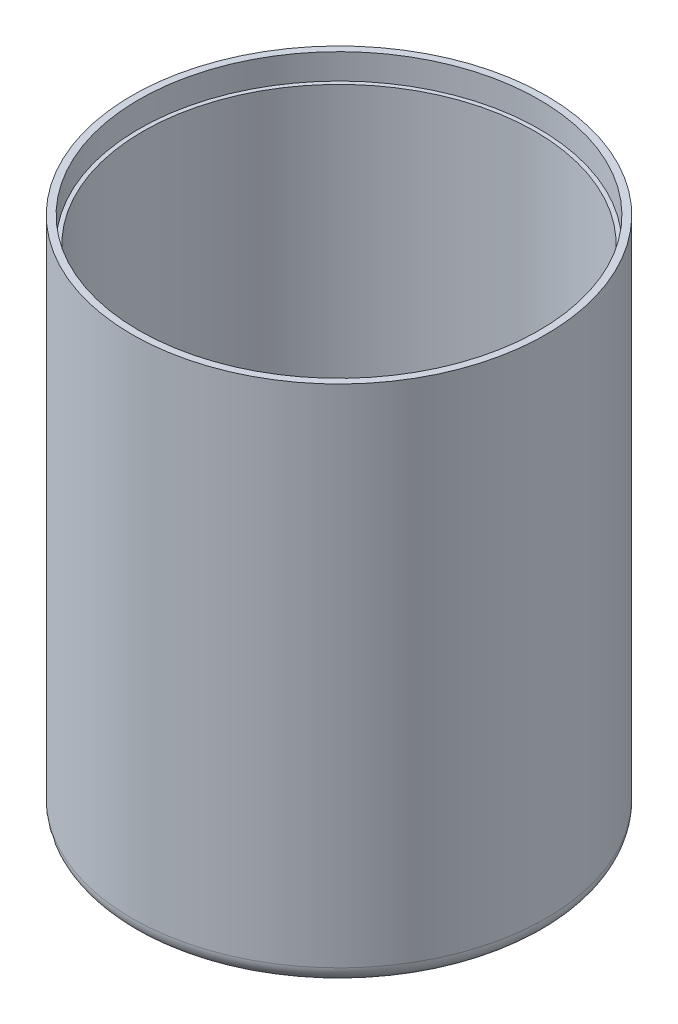
SolidWorks part; units mm, degrees
ref_plane "前视基准面" through (0, 0, 0) normal (0, 0, 1) x (1, 0, 0)
ref_plane "上视基准面" through (0, 0, 0) normal (0, 1, 0) x (1, 0, 0)
ref_plane "右视基准面" through (0, 0, 0) normal (1, 0, 0) x (0, 0, -1)
sketch "草图3" plane through (0, 0, 0) normal (0, 0, 1) x (1, 0, 0)
  line L0 (3.225, -1.7) -> (3.225, 0)
  line L1 (3.225, 0) -> (12.2, 0)
  line L2 (12.2, 0) -> (12.2, 30.8)
  line L3 (0, -2.2801) -> (0, 32.8942) construction
  dimension "D1" = 1.7
  dimension "D2" = 12.2
  dimension "D3" = 3.225
  dimension "D4" = 30.8
revolve "旋转-薄壁1" add sketch "草图3" angle 360 about L3 wall 0.65
sketch "草图8" plane through (0, 0, 0) normal (0, -1, 0) x (1, 0, 0)
  line L0 (0, -4.2367) -> (0, 3.6419) construction
  circle A0 centre (-8.5, 0) radius 1
  circle A1 centre (8.5, 0) radius 1
  dimension "D2" = 2
  dimension "D1" = 17
extrude "切除-拉伸1" cut sketch "草图8" against normal through all
sketch "草图9" plane through (0, 0, 0) normal (0, 0, 1) x (1, 0, 0)
  line L0 (-9.5, 0.65) -> (-9.5, 1.05)
  line L1 (-8.5, 2.0071) -> (-8.5, -0.8567) construction
  line L2 (-7.5, 0) -> (-7.5, 0.65) construction
  line L3 (-9.5, 0.65) -> (-9.5, 0) construction
  dimension "D1" = 0.4
revolve "旋转-薄壁2" add sketch "草图9" angle 360 about L1 wall 0.43
hole_wizard "M3 螺纹孔2" positions "草图11" profile "草图12" tap size "M3" standard "GB" end condition through all
sketch "草图11" plane through (0, 0, 0) normal (0, -1, 0) x (-1, 0, 0)
  point P0 (8.5, 0)
  point P3 (-8.5, 0)
sketch "草图12" plane through (-8.5, 0, 0) normal (1, 0, 0) x (0, 0, -1)
  line L0 (0, 0) -> (0, 30.8)
  line L1 (0, 30.8) -> (1.25, 30.8)
  line L2 (1.25, 30.8) -> (1.25, 0)
  line L5 (1.25, 0) -> (0, 0)
  line L11 (0, -6.35) -> (0, 107.95) construction
  dimension "通孔螺纹孔钻头直径" = 2.5
  dimension "通孔螺纹孔钻头深度" = 30.8
cosmetic thread "孔螺蚊线3" parameters "D2"=3
cosmetic thread "孔螺蚊线4" parameters "D2"=3
sketch "草图13" plane through (0, 30.8, 0) normal (0, 1, 0) x (1, 0, 0)
  circle A0 centre (0, 0) radius 11.79
  circle A1 centre (0, 0) radius 12.2 construction
  dimension "D1" = 0.41
extrude "切除-拉伸2" cut sketch "草图13" against normal blind 1.5
fillet "圆角1" radius 1 1 edges at (0, 0, -12.2)
